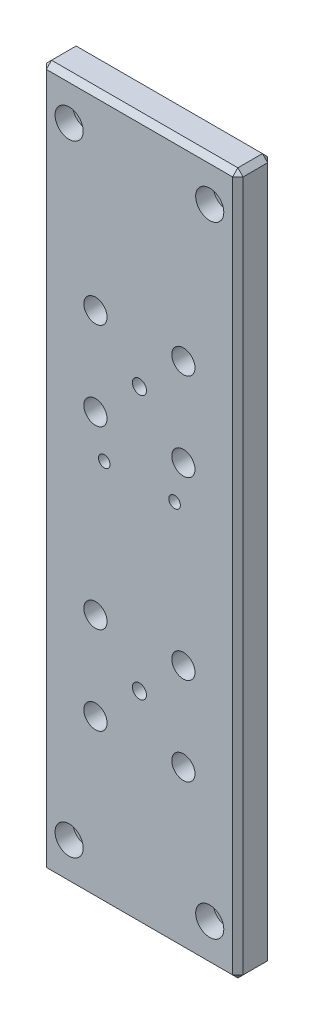
SolidWorks part; units mm, degrees
material "Aluminium - UNI EN 573 EN AW 6063"
ref_plane "Front Plane" through (0, 0, 0) normal (0, 0, 1) x (1, 0, 0)
ref_plane "Top Plane" through (0, 0, 0) normal (0, 1, 0) x (1, 0, 0)
ref_plane "Right Plane" through (0, 0, 0) normal (1, 0, 0) x (0, 0, -1)
sketch "Sketch1" plane through (0, 0, 0) normal (0, 0, 1) x (1, 0, 0)
  line L0 (26, 176.6) -> (-26, 176.6) construction
  line L1 (-28, -21.5) -> (28, -21.5)
  line L2 (-28, -21.5) -> (-28, 178.1)
  line L3 (-28, 178.1) -> (28, 178.1)
  line L4 (28, -21.5) -> (28, 178.1)
  line L8 (-26, -20) -> (26, -20) construction
  line L9 (-26.5, -19.5) -> (-26.5, -0.5) construction
  line L10 (26.5, -19.5) -> (26.5, -0.5) construction
  dimension "D1" = 1.5
  dimension "D2" = 1.5
  dimension "D3" = 1.5
  dimension "D4" = 1.5
extrude "Extrude1" add sketch "Sketch1" along normal blind 10
chamfer "Chamfer1" distance 1.5 angle 45 12 edges at (0, -21.5, 0) (28, 78.3, 0) (0, 178.1, 0) (-28, 78.3, 0) (-28, 178.1, 5) (0, 178.1, 10) (28, 178.1, 5) (-28, 78.3, 10) (-28, -21.5, 5) (0, -21.5, 10) (28, 78.3, 10) (28, -21.5, 5)
hole_wizard "HoleWzd1" positions "Sketch3" profile "Sketch2" legacy
sketch "Sketch3" plane through (-28, 98.3, 0) normal (0, 0, -1) x (-1, 0, 0)
  circle A11 centre (-40, 68.3) radius 2 construction
  circle A12 centre (-16, 68.3) radius 2 construction
  circle A13 centre (-16, -108.3) radius 2 construction
  circle A14 centre (-40, -108.3) radius 2 construction
  point P1 (-40, -108.3)
  point P2 (-16, -108.3)
  point P4 (-40, 68.3)
  point P6 (-16, 68.3)
sketch "Sketch2" plane through (12, -10, 0) normal (1, 0, 0) x (0, 1, 0)
  line L0 (0, 0) -> (0, 5)
  line L1 (0, 5) -> (2, 5)
  line L2 (2, 5) -> (2, 0)
  line L3 (2, 0) -> (0, 0)
  line L4 (0, 110) -> (0, -10) construction
  dimension "Diameter" = 4
  dimension "Depth" = 5
hole_wizard "HoleWzd4" positions "Sketch12" profile "Sketch11" hole size "M6" standard "ISO" end condition up to next
sketch "Sketch12" plane through (0, 0, 0) normal (0, 0, -1) x (-1, 0, 0)
  line L0 (28, 78.3) -> (-28, 78.3) construction
  line L1 (28, 176.6) -> (28, -20) construction
  line L2 (-28, -20) -> (-28, 176.6) construction
  line L3 (0, 74.1969) -> (0, 99.1969) construction
  line L4 (-12.5, 99.1969) -> (12.5, 99.1969) construction
  line L5 (0, 99.1969) -> (0, 124.1969) construction
  line L6 (-12.5, 124.1969) -> (12.5, 124.1969) construction
  line L7 (0, 74.1969) -> (0, 49.1969) construction
  line L8 (-12.5, 49.1969) -> (12.5, 49.1969) construction
  line L9 (0, 49.1969) -> (0, 24.1969) construction
  line L10 (-12.5, 24.1969) -> (12.5, 24.1969) construction
  point P0 (-12.5, 99.1969)
  point P1 (12.5, 124.1969)
  point P2 (-12.5, 124.1969)
  point P3 (12.5, 99.1969)
  point P4 (-12.5, 49.1969)
  point P5 (12.5, 49.1969)
  point P6 (12.5, 24.1969)
  point P7 (-12.5, 24.1969)
  dimension "D1" = 25
  dimension "D2" = 50
  dimension "D3" = 25
sketch "Sketch11" plane through (12.5, 99.1969, 0) normal (1, 0, 0) x (0, 1, 0)
  line L0 (0, 0) -> (0, 10)
  line L1 (0, 10) -> (3.3, 10)
  line L2 (3.3, 10) -> (3.3, 0)
  line L5 (3.3, 0) -> (0, 0)
  line L11 (0, -6.35) -> (0, 107.95) construction
  dimension "Thru Hole Dia." = 6.6
  dimension "Thru Hole Depth" = 10
hole_wizard "HoleWzd5" positions "Sketch14" profile "Sketch13" legacy end condition up to next
sketch "Sketch14" plane through (0, 0, 0) normal (0, 0, -1) x (-1, 0, 0)
  line L0 (-12.5, 24.1969) -> (12.5, 49.1969) construction
  line L1 (-12.5, 99.1969) -> (12.5, 124.1969) construction
  point P0 (0, 111.6969)
  point P1 (0, 36.6969)
sketch "Sketch13" plane through (0, 111.6969, 0) normal (1, 0, 0) x (0, 1, 0)
  line L0 (0, 0) -> (0, 10)
  line L1 (0, 10) -> (2, 10)
  line L2 (2, 10) -> (2, 0)
  line L3 (2, 0) -> (0, 0)
  line L4 (0, 110) -> (0, -10) construction
  dimension "Diameter" = 4
  dimension "Depth" = 10
hole_wizard "HoleWzd6" positions "Sketch16" profile "Sketch15" legacy
sketch "Sketch16" plane through (0, 0, 0) normal (0, 0, -1) x (-1, 0, 0)
  point P1 (17.5, 88.301)
  point P2 (-17.5, 88.301)
sketch "Sketch15" plane through (-17.5, 88.301, 0) normal (1, 0, 0) x (0, 1, 0)
  line L0 (0, 0) -> (0, 5)
  line L1 (0, 5) -> (2, 5)
  line L2 (2, 5) -> (2, 0)
  line L3 (2, 0) -> (0, 0)
  line L4 (0, 110) -> (0, -10) construction
  dimension "Diameter" = 4
  dimension "Depth" = 5
hole_wizard "HoleWzd7" positions "Sketch18" profile "Sketch17" tap size "M4x0.7" standard "ISO" end condition through all
sketch "Sketch18" plane through (0, 0, 0) normal (0, 0, -1) x (-1, 0, 0)
  point P0 (10, 88.301)
  point P1 (-10, 88.301)
cosmetic thread "Cosmetic Thread3" parameters "D2"=4
cosmetic thread "Cosmetic Thread4" parameters "D2"=4
sketch "Sketch17" plane through (-10, 88.301, 0) normal (1, 0, 0) x (0, 1, 0)
  line L0 (0, 0) -> (0, 10)
  line L1 (0, 10) -> (1.65, 10)
  line L2 (1.65, 10) -> (1.65, 0)
  line L5 (1.65, 0) -> (0, 0)
  line L11 (0, -6.35) -> (0, 107.95) construction
  dimension "Thru Tap Drill Dia." = 3.3
  dimension "Thru Tap Drill Depth" = 10
hole_wizard "HoleWzd9" positions "Sketch22" profile "Sketch21" counterbore size "M4" standard "ISO" end condition through all
sketch "Sketch22" plane through (0, 0, 10) normal (0, 0, 1) x (1, 0, 0)
  circle A0 centre (20, -10) radius 1.65 construction
  circle A1 centre (-20, -10) radius 1.65 construction
  circle A2 centre (-20, 166.6) radius 1.65 construction
  circle A3 centre (20, 166.6) radius 1.65 construction
  point P1 (20, -10)
  point P2 (-20, -10)
  point P4 (20, 166.6)
  point P6 (-20, 166.6)
sketch "Sketch21" plane through (20, -10, 10) normal (1, 0, 0) x (0, -1, 0)
  line L0 (0, 0) -> (0, 10)
  line L1 (0, 10) -> (2.25, 10)
  line L3 (2.25, 10) -> (2.25, 5)
  line L4 (2.25, 5) -> (4, 5)
  line L5 (4, 5) -> (4, 0)
  line L7 (4, 0) -> (0, 0)
  line L11 (0, -6.35) -> (0, 107.95) construction
  dimension "Thru Hole Dia." = 4.5
  dimension "Thru Hole Depth" = 10
  dimension "C'Bore Dia." = 8
  dimension "C'Bore Depth" = 5
